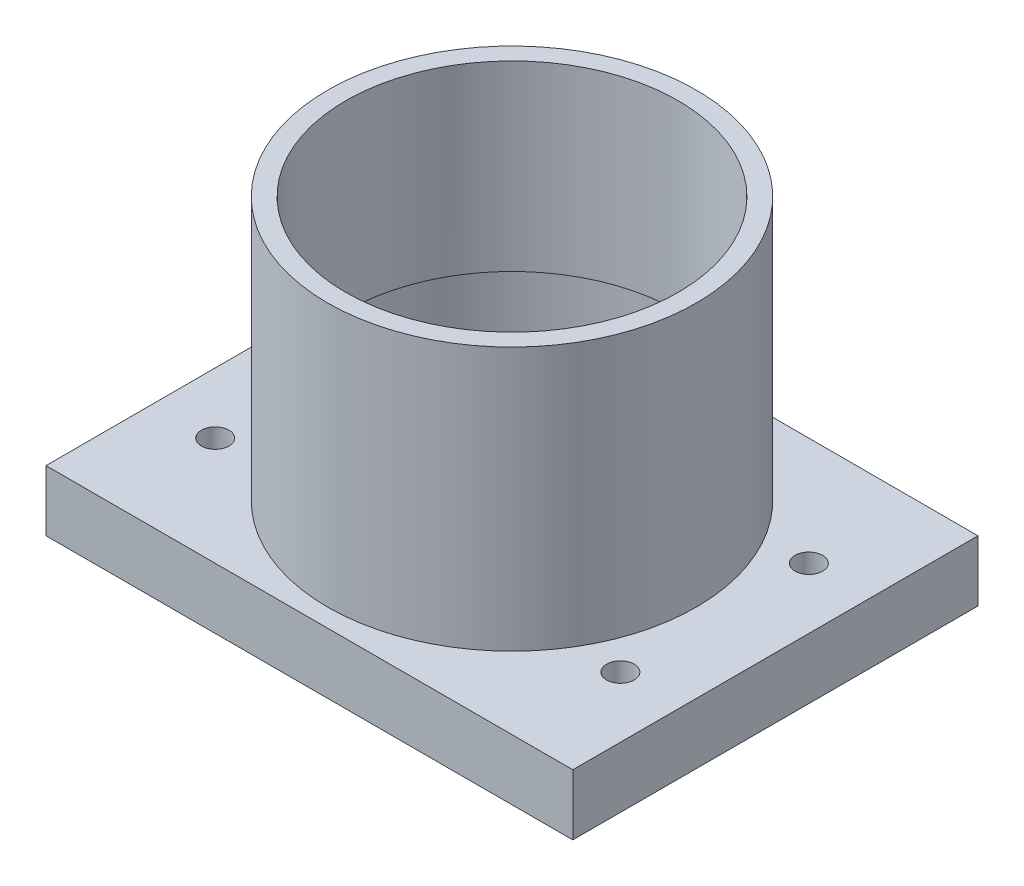
SolidWorks part; units mm, degrees
material "3003 Alloy"
ref_plane "Front Plane" through (0, 0, 0) normal (0, 0, 1) x (1, 0, 0)
ref_plane "Top Plane" through (0, 0, 0) normal (0, 1, 0) x (1, 0, 0)
ref_plane "Right Plane" through (0, 0, 0) normal (1, 0, 0) x (0, 0, -1)
sketch "Sketch1" plane through (0, 0, 0) normal (0, 1, 0) x (1, 0, 0)
  line L1 (-65, -50) -> (65, -50)
  line L2 (-65, -50) -> (-65, 50)
  line L3 (-65, 50) -> (65, 50)
  line L4 (65, -50) -> (65, 50)
  line L5 (-65, -50) -> (65, 50) construction
  line L6 (-65, 50) -> (65, -50) construction
  point P0 (0, 0)
  dimension "D1" = 130
  dimension "D2" = 100
extrude "Boss-Extrude1" add sketch "Sketch1" along normal blind 15
sketch "Sketch2" plane through (0, 15, 0) normal (0, 1, 0) x (1, 0, 0)
  circle A0 centre (0, 0) radius 45.5
  dimension "D1" = 91
extrude "Boss-Extrude2" add sketch "Sketch2" along normal blind 65
sketch "Sketch3" plane through (0, 80, 0) normal (0, 1, 0) x (1, 0, 0)
  circle A0 centre (0, 0) radius 41
  dimension "D1" = 82
extrude "Cut-Extrude1" cut sketch "Sketch3" against normal through all
sketch "Sketch4" plane through (0, 0, 0) normal (0, -1, 0) x (1, 0, 0)
  circle A0 centre (0, 0) radius 42.5
  dimension "D1" = 85
extrude "Cut-Extrude2" cut sketch "Sketch4" against normal blind 35
sketch "Sketch8" plane through (0, 15, 0) normal (0, 1, 0) x (1, 0, 0)
  line L0 (-50, 23.25) -> (50, 23.25) construction
  line L1 (50, 23.25) -> (50, -23.25) construction
  point P0 (-50, 23.25)
  point P1 (-50, -23.25)
  point P2 (50, 23.25)
  point P3 (50, -23.25)
  point P9 (0, 23.25)
  point P11 (50, 0)
  dimension "D1" = 100
  dimension "D2" = 46.5
hole_wizard "M8 Tapped Hole1" positions "Sketch9" profile "Sketch10" tap size "M8" standard "ISO"
sketch "Sketch9" plane through (0, 15, 0) normal (0, 1, 0) x (1, 0, 0)
  point P0 (-50, 23.25)
  point P3 (-50, -23.25)
  point P6 (50, -23.25)
  point P9 (50, 23.25)
sketch "Sketch10" plane through (-50, 15, -23.25) normal (1, 0, 0) x (0, 0, 1)
  line L0 (0, 0) -> (0, 19.75)
  line L1 (0, 19.75) -> (3.4, 17.7071)
  line L2 (3.4, 17.7071) -> (3.4, 0)
  line L5 (3.4, 0) -> (0, 0)
  line L10 (0, 19.75) -> (-3.4, 17.7071) construction
  line L11 (0, -6.35) -> (0, 107.95) construction
  dimension "Tap Drill Dia." = 6.8
  dimension "Tap Drill Depth" = 19.75
  dimension "Drill Angle" = 118
cosmetic thread "Hole Thread1" parameters "D1"=16, "D2"=8
cosmetic thread "Hole Thread2" parameters "D1"=16, "D2"=8
cosmetic thread "Hole Thread3" parameters "D1"=16, "D2"=8
cosmetic thread "Hole Thread4" parameters "D1"=16, "D2"=8
